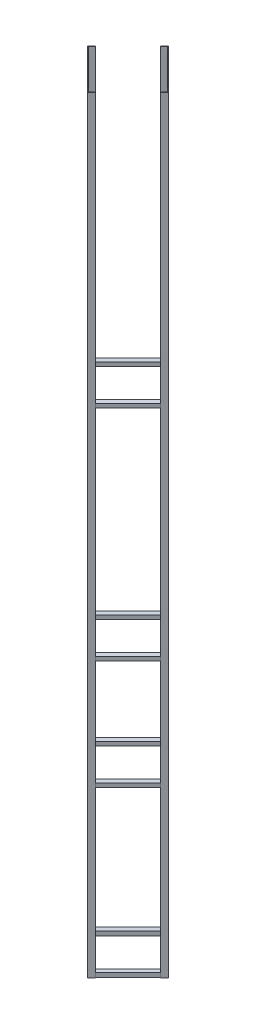
SolidWorks part; units mm, degrees
material "7075-T6 (SN)"
ref_plane "Front Plane" through (0, 0, 0) normal (0, 0, 1) x (1, 0, 0)
ref_plane "Top Plane" through (0, 0, 0) normal (0, 1, 0) x (1, 0, 0)
ref_plane "Right Plane" through (0, 0, 0) normal (1, 0, 0) x (0, 0, -1)
sketch "Sketch2" plane through (0, 0, 0) normal (0, 1, 0) x (1, 0, 0)
  line L0 (0, 93.5537) -> (-8.9803, 84.5734)
  line L1 (-8.9803, 84.5734) -> (-7.8577, 83.4509)
  line L2 (-7.8577, 83.4509) -> (0, 91.3086)
  line L3 (0, 91.3086) -> (7.8577, 83.4509)
  line L4 (7.8577, 83.4509) -> (8.9803, 84.5734)
  line L5 (8.9803, 84.5734) -> (0, 93.5537)
  line L6 (0, 0) -> (0, 186.644) construction
  line L7 (93.5537, 0) -> (84.5734, 8.9803)
  line L8 (84.5734, 8.9803) -> (83.4509, 7.8577)
  line L9 (83.4509, 7.8577) -> (91.3086, 0)
  line L10 (91.3086, 0) -> (83.4509, -7.8577)
  line L11 (83.4509, -7.8577) -> (84.5734, -8.9803)
  line L12 (84.5734, -8.9803) -> (93.5537, 0)
  line L13 (0, -93.5537) -> (8.9803, -84.5734)
  line L14 (8.9803, -84.5734) -> (7.8577, -83.4509)
  line L15 (7.8577, -83.4509) -> (0, -91.3086)
  line L16 (0, -91.3086) -> (-7.8577, -83.4509)
  line L17 (-7.8577, -83.4509) -> (-8.9803, -84.5734)
  line L18 (-8.9803, -84.5734) -> (0, -93.5537)
  line L19 (-93.5537, 0) -> (-84.5734, -8.9803)
  line L20 (-84.5734, -8.9803) -> (-83.4509, -7.8577)
  line L21 (-83.4509, -7.8577) -> (-91.3086, 0)
  line L22 (-91.3086, 0) -> (-83.4509, 7.8577)
  line L23 (-83.4509, 7.8577) -> (-84.5734, 8.9803)
  line L24 (-84.5734, 8.9803) -> (-93.5537, 0)
  point P31 (0, 0)
  dimension "D2" = 12.7
  dimension "D3" = 12.7
  dimension "D4" = 1.5875
  dimension "D5" = 1.5875
extrude "Boss-Extrude6" add sketch "Sketch2" along normal blind 1778
sketch "Sketch11" plane through (-45.6543, 0, -45.6543) normal (0.7071, 0, 0.7071) x (0.7071, 0, -0.7071)
  line L0 (-53.4524, 1778) -> (-53.4524, 0) construction
  line L1 (-64.5649, 0) -> (-53.4524, 0)
  line L2 (-64.5649, 0) -> (-64.5649, 9.525)
  line L3 (-64.5649, 9.525) -> (-53.4524, 9.525)
  line L4 (-53.4524, 0) -> (-53.4524, 9.525)
  dimension "D1" = 9.525
extrude "Boss-Extrude11" add sketch "Sketch11" along normal up to next (129.1299 mm away)
sketch "Sketch13" plane through (-37.7966, 0, 37.7966) normal (0.7071, 0, -0.7071) x (-0.7071, 0, -0.7071)
  line L0 (-66.1524, 0) -> (66.1524, 0) construction
  line L1 (-64.5649, 9.525) -> (-53.4524, 9.525)
  line L2 (-64.5649, 9.525) -> (-64.5649, 0)
  line L3 (-64.5649, 0) -> (-53.4524, 0)
  line L4 (-53.4524, 9.525) -> (-53.4524, 0)
  dimension "D1" = 11.1125
extrude "Boss-Extrude13" add sketch "Sketch13" along normal up to next (118.0174 mm away)
sketch "Sketch14" plane through (37.7966, 0, 37.7966) normal (-0.7071, 0, -0.7071) x (-0.7071, 0, 0.7071)
  line L0 (-66.1524, 0) -> (53.4524, 0) construction
  line L1 (-64.5649, 9.525) -> (-53.4524, 9.525)
  line L2 (-64.5649, 9.525) -> (-64.5649, 0)
  line L3 (-64.5649, 0) -> (-53.4524, 0)
  line L4 (-53.4524, 9.525) -> (-53.4524, 0)
  dimension "D1" = 11.1125
extrude "Boss-Extrude14" add sketch "Sketch14" along normal up to next (119.6049 mm away)
sketch "Sketch15" plane through (37.7966, 0, -37.7966) normal (-0.7071, 0, 0.7071) x (0.7071, 0, 0.7071)
  line L0 (-66.1524, 0) -> (53.4524, 0) construction
  line L1 (-64.5649, 9.525) -> (-53.4524, 9.525)
  line L2 (-64.5649, 9.525) -> (-64.5649, 0)
  line L3 (-64.5649, 0) -> (-53.4524, 0)
  line L4 (-53.4524, 9.525) -> (-53.4524, 0)
  dimension "D1" = 11.1125
extrude "Boss-Extrude15" add sketch "Sketch15" along normal up to next (106.9049 mm away)
pattern_linear "LPattern1" count 2 spacing 381 along (0, 1, 0) of "Boss-Extrude15", "Boss-Extrude14", "Boss-Extrude11", "Boss-Extrude13"
pattern_linear "LPattern2" count 2 spacing 635 along (0, 1, 0) of "Boss-Extrude15", "Boss-Extrude14", "Boss-Extrude13", "Boss-Extrude11"
pattern_linear "LPattern3" count 2 spacing 1143 along (0, 1, 0) of "Boss-Extrude11", "Boss-Extrude13", "Boss-Extrude14", "Boss-Extrude15"
sketch "Sketch16" plane through (-46.7768, 0, 46.7768) normal (-0.7071, 0, 0.7071) x (0.7071, 0, 0.7071)
  line L0 (-53.4524, 1778) -> (-53.4524, 0) construction
  line L1 (-66.1524, 1778) -> (-53.4524, 1778)
  line L2 (-66.1524, 1778) -> (-66.1524, 1765.3)
  line L3 (-66.1524, 1765.3) -> (-53.4524, 1765.3)
  line L4 (-53.4524, 1778) -> (-53.4524, 1765.3)
  dimension "D1" = 12.7
extrude "Boss-Extrude16" add sketch "Sketch16" along normal blind 0.0254
sketch "Sketch17" plane through (-46.7768, 0, 46.7768) normal (-0.7071, 0, 0.7071) x (0.7071, 0, 0.7071)
  line L0 (66.1524, 1778) -> (66.1524, 0) construction
  line L1 (53.4524, 1778) -> (66.1524, 1778)
  line L2 (53.4524, 1778) -> (53.4524, 1765.3)
  line L3 (53.4524, 1765.3) -> (66.1524, 1765.3)
  line L4 (66.1524, 1778) -> (66.1524, 1765.3)
  dimension "D1" = 12.7
extrude "Boss-Extrude17" add sketch "Sketch17" along normal blind 0.0254
sketch "Sketch18" plane through (37.7966, 0, -37.7966) normal (-0.7071, 0, 0.7071) x (0.7071, 0, 0.7071)
  line L0 (-64.5649, 1778) -> (-64.5649, 1152.525) construction
  line L1 (-66.1524, 1778) -> (-64.5649, 1778)
  line L2 (-66.1524, 1778) -> (-66.1524, 1765.3)
  line L3 (-66.1524, 1765.3) -> (-64.5649, 1765.3)
  line L4 (-64.5649, 1778) -> (-64.5649, 1765.3)
  dimension "D1" = 12.7
extrude "Boss-Extrude18" add sketch "Sketch18" along normal blind 0.0254
sketch "Sketch19" plane through (37.7966, 0, -37.7966) normal (-0.7071, 0, 0.7071) x (0.7071, 0, 0.7071)
  line L0 (64.5649, 1778) -> (66.1524, 1778) construction
  line L1 (64.5649, 1778) -> (66.1524, 1778)
  line L2 (64.5649, 1778) -> (64.5649, 1765.3)
  line L3 (64.5649, 1765.3) -> (66.1524, 1765.3)
  line L4 (66.1524, 1778) -> (66.1524, 1765.3)
  line L5 (64.5649, 1778) -> (64.5649, 1152.525) construction
  line L6 (66.1524, 1778) -> (66.1524, 0) construction
  dimension "D1" = 12.7
extrude "Boss-Extrude19" add sketch "Sketch19" along normal blind 0.0254
